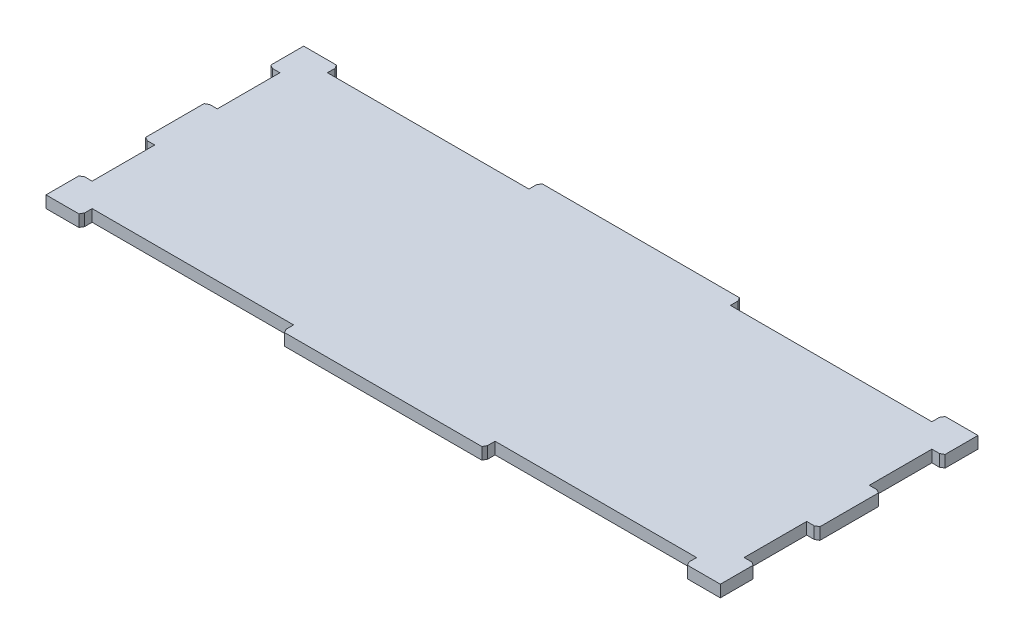
SolidWorks part; units mm, degrees
ref_plane "Front Plane" through (0, 0, 0) normal (0, 0, 1) x (1, 0, 0)
ref_plane "Top Plane" through (0, 0, 0) normal (0, 1, 0) x (1, 0, 0)
ref_plane "Right Plane" through (0, 0, 0) normal (1, 0, 0) x (0, 0, -1)
sketch "Sketch1" plane through (0, 0, 0) normal (0, 1, 0) x (1, 0, 0)
  line L0 (-96.8316, 0) -> (-122.555, 0) construction
  line L1 (-122.555, 46.8266) -> (122.555, 46.8266)
  line L2 (-122.555, 46.8266) -> (-122.555, -46.8266)
  line L3 (-122.555, -46.8266) -> (122.555, -46.8266)
  line L4 (122.555, 46.8266) -> (122.555, -46.8266)
  line L5 (-122.555, 46.8266) -> (122.555, -46.8266) construction
  line L6 (-122.555, -46.8266) -> (122.555, 46.8266) construction
  line L7 (96.8316, -21.1031) -> (-96.8316, -21.1031) construction
  line L8 (96.8316, -21.1031) -> (96.8316, 21.1031) construction
  line L9 (96.8316, 21.1031) -> (-96.8316, 21.1031) construction
  line L10 (-96.8316, -21.1031) -> (-96.8316, 21.1031) construction
  line L11 (96.8316, -21.1031) -> (-96.8316, 21.1031) construction
  line L12 (96.8316, 21.1031) -> (-96.8316, -21.1031) construction
  line L13 (0, 21.1031) -> (0, 46.8266) construction
  point P0 (0, 0)
  point P6 (0, 0)
  dimension "D1" = 93.6531
  dimension "D2" = 245.11
  dimension "D3" = 25.7234
extrude "Boss-Extrude1" add sketch "Sketch1" along normal blind 4.318
sketch "Sketch2" plane through (0, 4.318, 0) normal (0, 1, 0) x (1, 0, 0)
  line L0 (122.555, 46.8266) -> (-122.555, 46.8266) construction
  line L5 (-122.555, 34.1266) -> (-118.491, 34.1266)
  line L10 (-122.555, 46.8266) -> (-122.555, -46.8266) construction
  line L15 (-122.555, 34.1266) -> (-122.555, 11.3755)
  line L20 (122.555, -46.8266) -> (122.555, 46.8266) construction
  line L21 (-122.555, 11.3755) -> (-118.491, 11.3755)
  line L22 (-122.555, -46.8266) -> (122.555, -46.8266) construction
  line L23 (-109.855, -46.8266) -> (-36.6183, -46.8266)
  line L24 (-109.855, -46.8266) -> (-109.855, -42.7626)
  line L25 (-109.855, -42.7626) -> (-36.6183, -42.7626)
  line L26 (-36.6183, -46.8266) -> (-36.6183, -42.7626)
  line L27 (-36.6183, -44.7946) -> (36.6183, -44.7946) construction
  line L28 (36.6183, -46.8266) -> (109.855, -46.8266)
  line L29 (36.6183, -46.8266) -> (36.6183, -42.7626)
  line L30 (36.6183, -42.7626) -> (109.855, -42.7626)
  line L31 (109.855, -46.8266) -> (109.855, -42.7626)
  line L32 (-109.855, -44.7946) -> (-122.555, -44.7946) construction
  line L33 (-118.491, 34.1266) -> (-118.491, 11.3755)
  line L34 (-122.555, -11.3755) -> (-118.491, -11.3755)
  line L35 (109.855, -44.7946) -> (122.555, -44.7946) construction
  line L36 (-122.555, -11.3755) -> (-122.555, -34.1266)
  line L37 (-122.555, -34.1266) -> (-118.491, -34.1266)
  line L38 (-118.491, -11.3755) -> (-118.491, -34.1266)
  line L39 (-109.855, 46.8266) -> (-36.6183, 46.8266)
  line L40 (-109.855, 46.8266) -> (-109.855, 42.7626)
  line L41 (-109.855, 42.7626) -> (-36.6183, 42.7626)
  line L42 (-36.6183, 46.8266) -> (-36.6183, 42.7626)
  line L43 (120.523, 34.1266) -> (120.523, 46.8266) construction
  line L44 (36.6183, 46.8266) -> (109.855, 46.8266)
  line L45 (36.6183, 46.8266) -> (36.6183, 42.7626)
  line L46 (36.6183, 42.7626) -> (109.855, 42.7626)
  line L47 (109.855, 46.8266) -> (109.855, 42.7626)
  line L48 (122.555, 34.1266) -> (118.491, 34.1266)
  line L49 (122.555, 34.1266) -> (122.555, 11.3755)
  line L50 (122.555, 11.3755) -> (118.491, 11.3755)
  line L51 (118.491, 34.1266) -> (118.491, 11.3755)
  line L52 (122.555, -11.3755) -> (118.491, -11.3755)
  line L53 (122.555, -11.3755) -> (122.555, -34.1266)
  line L54 (122.555, -34.1266) -> (118.491, -34.1266)
  line L55 (118.491, -11.3755) -> (118.491, -34.1266)
  line L56 (120.523, 11.3755) -> (120.523, -11.3755) construction
  line L57 (120.523, -34.1266) -> (120.523, -46.8266) construction
  line L58 (-120.523, 34.1266) -> (-120.523, 46.8266) construction
  line L59 (-109.855, 44.7946) -> (-122.555, 44.7946) construction
  line L60 (-36.6183, 44.7946) -> (36.6183, 44.7946) construction
  line L61 (109.855, 44.7946) -> (122.555, 44.7946) construction
  line L62 (-120.523, 11.3755) -> (-120.523, -11.3755) construction
  line L63 (-120.523, -34.1266) -> (-120.523, -46.8266) construction
  dimension "D1" = 12.7
  dimension "D2" = 12.7
  dimension "D3" = 12.7
  dimension "D4" = 4.064
  dimension "D5" = 12.7
extrude "Cut-Extrude1" cut sketch "Sketch2" against normal up to next
sketch "Sketch3" plane through (0, 4.318, 0) normal (0, 1, 0) x (1, 0, 0)
  line L0 (36.6183, 46.8266) -> (-36.6183, 46.8266) construction
  line L1 (118.491, 34.1266) -> (118.491, 11.3755) construction
  line L6 (-74.93, 47.0806) -> (-74.93, 40.4766) construction
  line L7 (109.855, -42.7626) -> (36.6183, -42.7626) construction
  line L8 (-59.817, 40.4766) -> (-113.157, 40.4766)
  line L9 (-113.157, 40.4766) -> (-113.157, -25.5634)
  line L10 (-113.157, -25.5634) -> (-110.617, -25.5634)
  line L11 (-110.617, -25.5634) -> (-108.077, -28.1034)
  line L12 (-108.077, -28.1034) -> (-75.311, -28.1034)
  line L13 (-75.311, -28.1034) -> (-72.771, -25.5634)
  line L14 (-72.771, -25.5634) -> (-59.817, -25.5634)
  line L15 (-59.817, -25.5634) -> (-59.817, 40.4766)
  line L16 (-105.537, -25.5634) -> (-77.597, -25.5634) construction
  line L17 (-62.357, 25.2366) -> (-110.617, 26.5066) construction
  line L18 (-68.834, 40.4766) -> (-68.834, 47.0806)
  line L19 (-68.834, 47.0806) -> (-81.026, 47.0806)
  line L20 (-81.026, 40.4766) -> (-81.026, 47.0806)
  line L21 (-100.33, 40.4766) -> (-100.33, 42.6356)
  line L22 (-100.33, 42.6356) -> (-109.22, 42.6356)
  line L23 (-109.22, 40.4766) -> (-109.22, 42.6356)
  line L24 (82.3849, 41.402) -> (82.3849, 42.7626) construction
  line L25 (36.6183, 42.7626) -> (109.855, 42.7626) construction
  line L26 (82.3849, -41.402) -> (82.3849, -42.7626) construction
  line L27 (-122.555, 46.8266) -> (-122.555, 34.1266) construction
  line L28 (-103.505, -28.1034) -> (-103.505, -42.7626) construction
  line L29 (-36.6183, -42.7626) -> (-109.855, -42.7626) construction
  line L30 (-122.555, -34.1266) -> (-122.555, -46.8266) construction
  line L34 (109.093, 41.402) -> (109.093, -41.402)
  line L35 (109.093, 41.402) -> (55.6768, 41.402)
  line L36 (55.6768, 41.402) -> (55.6768, -41.402)
  line L37 (109.093, -41.402) -> (55.6768, -41.402)
  line L40 (55.6768, -41.402) -> (64.9478, -41.402)
  line L41 (64.9478, -41.402) -> (64.9478, -47.752)
  line L42 (109.093, 41.402) -> (99.822, 41.402)
  line L43 (99.822, 41.402) -> (99.822, 47.752)
  line L44 (109.093, 47.752) -> (99.822, 47.752)
  line L45 (109.093, 41.402) -> (109.093, 32.131)
  line L46 (115.443, 41.402) -> (115.443, 32.131)
  line L47 (109.093, 32.131) -> (115.443, 32.131)
  line L48 (55.6768, -41.402) -> (55.6768, -32.131)
  line L49 (49.3268, -41.402) -> (49.3268, -32.131)
  line L50 (55.6768, -32.131) -> (49.3268, -32.131)
  line L51 (55.6768, -47.752) -> (64.9478, -47.752)
  line L52 (53.6448, -41.402) -> (53.6448, -32.131) construction
  line L53 (55.6768, -43.434) -> (64.9478, -43.434) construction
  line L54 (60.3123, -43.434) -> (60.3123, -45.593) construction
  line L55 (60.3123, -45.593) -> (60.3123, -47.752) construction
  line L56 (53.6448, -36.7665) -> (51.4858, -36.7665) construction
  line L57 (51.4858, -36.7665) -> (49.3268, -36.7665) construction
  line L58 (53.6448, -36.7665) -> (55.6768, -36.7665) construction
  line L59 (60.3123, -43.434) -> (60.3123, -41.402) construction
  line L60 (111.125, 32.131) -> (111.125, 41.402) construction
  line L61 (109.093, 43.434) -> (99.822, 43.434) construction
  line L62 (104.4575, 47.752) -> (104.4575, 45.593) construction
  line L63 (104.4575, 45.593) -> (104.4575, 43.434) construction
  line L64 (104.4575, 43.434) -> (104.4575, 41.402) construction
  line L65 (115.443, 36.7665) -> (113.284, 36.7665) construction
  line L66 (113.284, 36.7665) -> (111.125, 36.7665) construction
  line L67 (111.125, 36.7665) -> (109.093, 36.7665) construction
  line L68 (55.6768, -47.752) -> (55.6768, -41.402)
  line L69 (55.6768, -41.402) -> (49.3268, -41.402)
  line L70 (109.093, 41.402) -> (109.093, 47.752)
  line L71 (109.093, 41.402) -> (115.443, 41.402)
  circle A0 centre (-77.597, -25.5634) radius 1.524
  circle A1 centre (-105.537, -25.5634) radius 1.524
  circle A2 centre (-110.617, 26.5066) radius 1.524
  circle A3 centre (-62.357, 25.2366) radius 1.524
  dimension "D9" = 3.048
  dimension "D3" = 0.254
  dimension "D4" = 53.34
  dimension "D5" = 68.58
  dimension "D6" = 12.954
  dimension "D7" = 2.54
  dimension "D8" = 2.54
  dimension "D10" = 13.97
  dimension "D11" = 27.94
  dimension "D12" = 45
  dimension "D13" = 45
  dimension "D14" = 2.54
  dimension "D15" = 12.192
  dimension "D16" = 8.89
  dimension "D17" = 3.937
  dimension "D18" = 2.159
  dimension "D19" = 9.017
  dimension "D20" = 6.604
  dimension "D21" = 1.27
  dimension "D22" = 48.26
  dimension "D23" = 5.08
  dimension "D24" = 52.07
  dimension "D25" = 82.804
  dimension "D26" = 53.4162
  dimension "D27" = 2.032
  dimension "D28" = 6.35
  dimension "D29" = 6.35
  dimension "D30" = 9.271
  dimension "D31" = 3.048
  dimension "D32" = 47.625
  dimension "D33" = 19.05
chamfer "Chamfer1" distance 0.762 angle 60 8 edges at (-109.855, 2.159, 46.8266) (36.6183, 2.159, 46.8266) (-36.6183, 2.159, -46.8266) (-122.555, 2.159, -34.1266) (-122.555, 2.159, 11.3755) (122.555, 2.159, 34.1266) (122.555, 2.159, -11.3755) (109.855, 2.159, -46.8266)
chamfer "Chamfer2" distance 0.762 angle 60 8 edges at (109.855, 2.159, 46.8266) (-36.6183, 2.159, 46.8266) (-122.555, 2.159, 34.1266) (-122.555, 2.159, -11.3755) (-109.855, 2.159, -46.8266) (36.6183, 2.159, -46.8266) (122.555, 2.159, -34.1266) (122.555, 2.159, 11.3755)
ref_plane "Plane1" through (-109.855, 4.318, 42.7626) normal (0, 0, 1) x (1, 0, 0)
